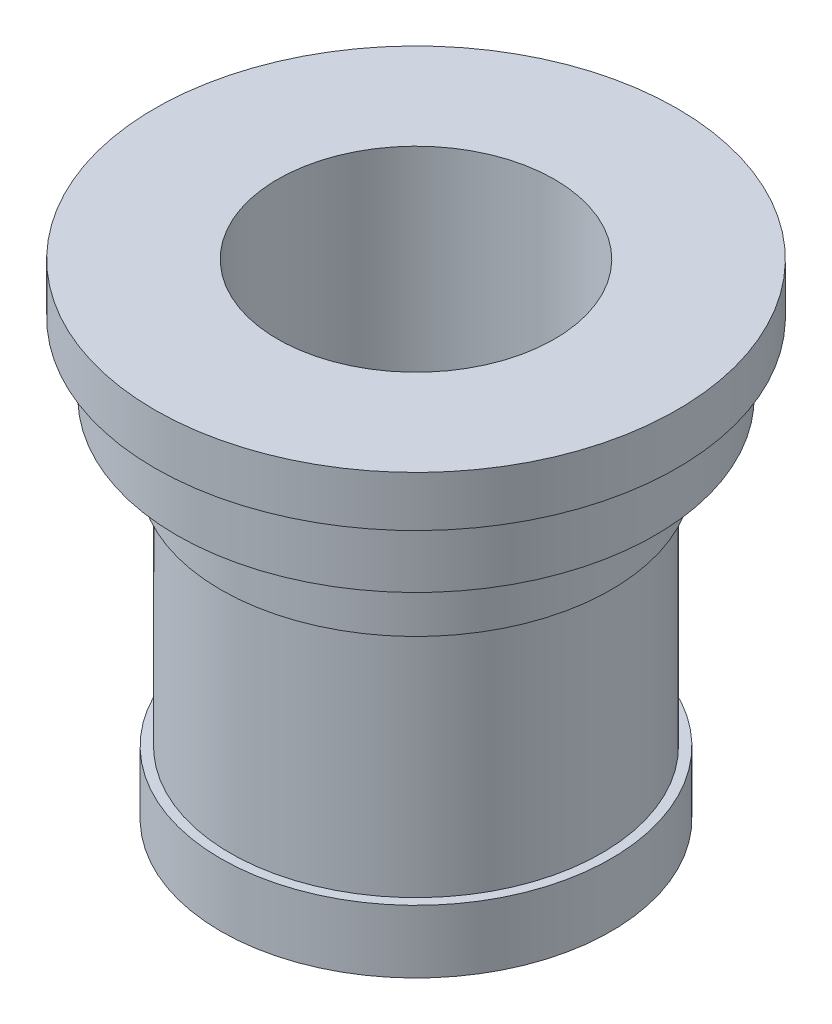
SolidWorks part; units mm, degrees
ref_plane "Front Plane" through (0, 0, 0) normal (0, 0, 1) x (1, 0, 0)
ref_plane "Top Plane" through (0, 0, 0) normal (0, 1, 0) x (1, 0, 0)
ref_plane "Right Plane" through (0, 0, 0) normal (1, 0, 0) x (0, 0, -1)
sketch "Sketch1" plane through (0, 0, 0) normal (0, 0, 1) x (1, 0, 0)
  line L0 (0, 0) -> (0, 50000) construction
  line L1 (0, 0) -> (50000, 0) construction
  line L2 (22, 50.2379) -> (22, -26.7621)
  line L3 (22, -26.7621) -> (31, -26.7621)
  line L4 (31, -26.7621) -> (31, -16.7621)
  line L5 (31, -16.7621) -> (29.5, -16.7621)
  line L6 (29.5, -16.7621) -> (29.5, 20.2379)
  line L7 (29.5, 20.2379) -> (31, 20.2379)
  line L8 (31, 20.2379) -> (31, 31.2379)
  line L9 (38, 42.2379) -> (41.5, 42.2379)
  line L10 (41.5, 42.2379) -> (41.5, 50.2379)
  line L11 (41.5, 50.2379) -> (22, 50.2379)
  line L12 (31, 31.2379) -> (38, 31.2379)
  line L13 (38, 31.2379) -> (38, 42.2379)
  dimension "D1" = 22
  dimension "D2" = 31
  dimension "D3" = 29.5
  dimension "D4" = 31
  dimension "D5" = 41.5
  dimension "D6" = 38
  dimension "D7" = 8
  dimension "D8" = 11
  dimension "D9" = 11
  dimension "D10" = 37
  dimension "D11" = 10
  dimension "D12" = 77
revolve "Revolve1" add sketch "Sketch1" angle 360 about L0
